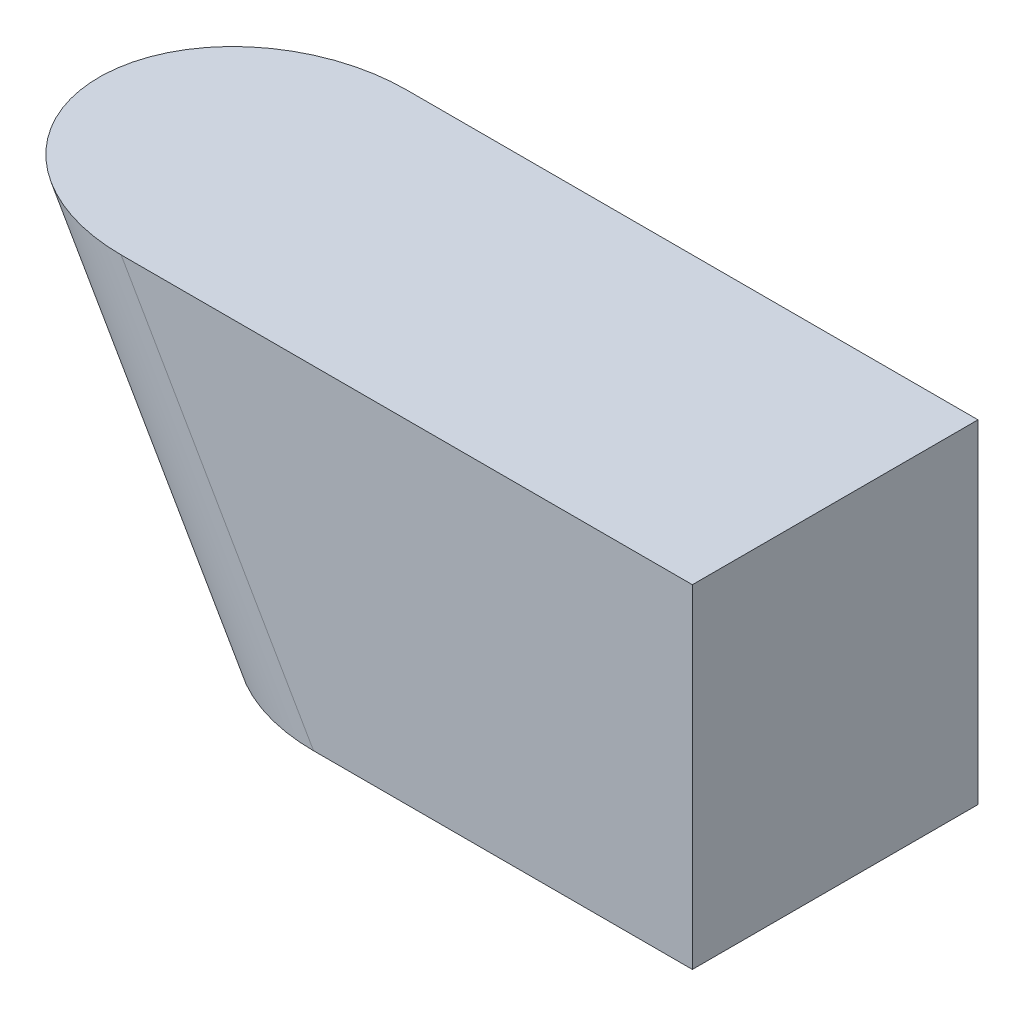
SolidWorks part; units mm, degrees
ref_plane "Ebene vorne" through (0, 0, 0) normal (0, 0, 1) x (1, 0, 0)
ref_plane "Ebene oben" through (0, 0, 0) normal (0, 1, 0) x (1, 0, 0)
ref_plane "Ebene rechts" through (0, 0, 0) normal (1, 0, 0) x (0, 0, -1)
sketch "Skizze1" plane through (0, 0, 0) normal (0, 0, 1) x (1, 0, 0)
  line L0 (0, 0) -> (-202.0726, 350)
  line L1 (-202.0726, 350) -> (397.9274, 350)
  line L2 (397.9274, 350) -> (397.9274, 0)
  line L3 (397.9274, 0) -> (0, 0)
  dimension "D1" = 600
  dimension "D2" = 350
  dimension "D3" = 60
extrude "Aufsatz-Linear austragen1" add sketch "Skizze1" along normal mid plane 300
ref_plane "Ebene1" through (-202.0726, 350, 0) normal (-0.5, 0.866, 0) x (0, 0, -1)
sketch "Skizze3" plane through (-202.0726, 350, 0) normal (-0.5, 0.866, 0) x (0, 0, -1)
  line L0 (-150, 0) -> (150, 0) construction
  line L1 (150, 0) -> (-150, 0)
  circle A0 centre (0, 0) radius 150 construction
  arc A1 (150, 0) -> (-150, 0) centre (0, 0) ccw
extrude "Aufsatz-Linear austragen2" add sketch "Skizze3" against normal up to surface and the other way up to surface up to face at (198.9637, 0, 0) other way up to face at (97.9274, 350, 0)
